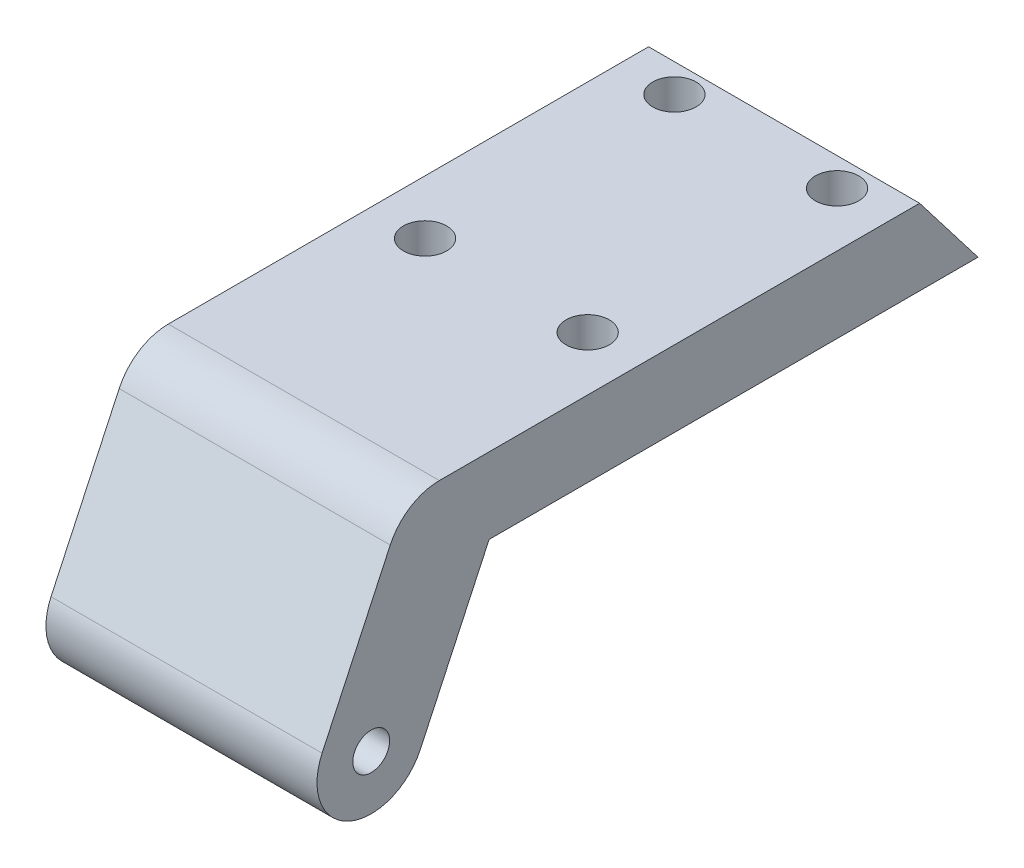
SolidWorks part; units mm, degrees
ref_plane "Спереди" through (0, 0, 0) normal (0, 0, 1) x (1, 0, 0)
ref_plane "Сверху" through (0, 0, 0) normal (0, 1, 0) x (1, 0, 0)
ref_plane "Справа" through (0, 0, 0) normal (1, 0, 0) x (0, 0, -1)
sketch "Эскиз1" plane through (0, 0, 0) normal (0, 1, 0) x (1, 0, 0)
  line L0 (1264.5856, -1638.1371) -> (1239.5856, -1638.1371) construction
  line L1 (1239.5856, -1588.2126) -> (1264.5856, -1588.2126)
  line L2 (1239.5856, -1588.2126) -> (1239.5856, -1632.1226)
  line L3 (1239.5856, -1632.1226) -> (1264.5856, -1632.1226)
  line L4 (1264.5856, -1588.2126) -> (1264.5856, -1632.1226)
  line L5 (1264.5856, -1594.2313) -> (1239.5856, -1594.2313) construction
  line L6 (1264.5856, -1638.1371) -> (1264.5856, -1594.2313) construction
  line L7 (1239.5856, -1638.1371) -> (1239.5856, -1594.2313) construction
  point P8 (1252.0856, -1594.2313)
  dimension "D1" = 43.9058
  dimension "D2" = 43.91
  dimension "D3" = 43.9058
  dimension "D4" = 25
  dimension "D5" = 25
extrude "Бобышка-Вытянуть1" add sketch "Эскиз1" along normal blind 7
sketch "Эскиз2" plane through (1264.5856, 0, 0) normal (1, 0, 0) x (0, 0, -1)
  line L0 (-1594.2313, 0) -> (-1599.6131, 7)
  line L2 (-1632.1226, 0) -> (-1588.2126, 0) construction
  line L4 (-1632.1226, 7) -> (-1588.2126, 7) construction
  line L5 (-1599.6131, 7) -> (-1588.1275, 9.9484)
  line L6 (-1588.1275, 9.9484) -> (-1585.313, -1.0155)
  line L7 (-1585.313, -1.0155) -> (-1594.2313, 0)
  point P2 (-1588.2126, 0)
  point P8 (-1594.2313, 0)
  point P13 (-1586.8388, 5.6836)
  point P14 (-1585.313, -1.0155)
  dimension "D1" = 307.554
  dimension "D2" = 8.8297
  dimension "D3" = 11.4006
  dimension "D4" = 8.9183
  dimension "D5" = 10.964
  dimension "D6" = 11.4856
extrude "Вырез-Вытянуть1" cut sketch "Эскиз2" against normal blind 65
sketch "Эскиз3" plane through (0, 7, 0) normal (0, 1, 0) x (1, 0, 0)
  line L1 (1264.5856, -1632.1226) -> (1264.5856, -1599.6131) construction
  line L2 (1239.5856, -1599.6131) -> (1239.5856, -1632.1226) construction
  line L4 (1264.5856, -1594.2313) -> (1239.5856, -1594.2313) construction
  circle A0 centre (1259.5856, -1602.2313) radius 2
  circle A1 centre (1259.5856, -1625.2313) radius 2
  circle A2 centre (1244.5856, -1602.2313) radius 2
  circle A3 centre (1244.5856, -1625.2313) radius 2
  dimension "D1" = 4
  dimension "D2" = 4
  dimension "D3" = 4
  dimension "D4" = 4
  dimension "D5" = 8
  dimension "D6" = 5
  dimension "D7" = 5
  dimension "D8" = 23
extrude "Вырез-Вытянуть2" cut sketch "Эскиз3" against normal blind 65
sketch "Эскиз4" plane through (0, 0, 1632.1226) normal (0, 0, 1) x (1, 0, 0)
  line L1 (1239.5856, 7) -> (1264.5856, 7)
  line L2 (1239.5856, 7) -> (1239.5856, 0)
  line L3 (1239.5856, 0) -> (1264.5856, 0)
  line L4 (1264.5856, 7) -> (1264.5856, 0)
extrude "Бобышка-Вытянуть2" add sketch "Эскиз4" along normal blind 10
sketch "Эскиз5" plane through (1264.5856, 0, 0) normal (1, 0, 0) x (0, 0, -1)
  line L0 (-1650.1934, -11.4815) -> (-1666.7871, -11.4815) construction
  line L1 (-1645.6618, -13.5946) -> (-1639.3226, 0)
  line L2 (-1642.1226, 0) -> (-1594.2313, 0) construction
  line L3 (-1642.1226, 7) -> (-1647.0922, 7)
  line L4 (-1647.0922, 7) -> (-1654.7249, -9.3684)
  line L5 (-1639.3226, 0) -> (-1642.1226, 7)
  arc A0 (-1654.7249, -9.3684) -> (-1645.6618, -13.5946) centre (-1650.1934, -11.4815) ccw
  circle A1 centre (-1650.1934, -11.4815) radius 1.7
  dimension "D1" = 10
  dimension "D2" = 3.4
  dimension "D3" = 15
  dimension "D4" = 2.8
  dimension "D5" = 115
extrude "Бобышка-Вытянуть3" add sketch "Эскиз5" against normal blind 25
fillet "Скругление1" radius 5 1 edges at (1252.0856, 7, 1647.0922)
